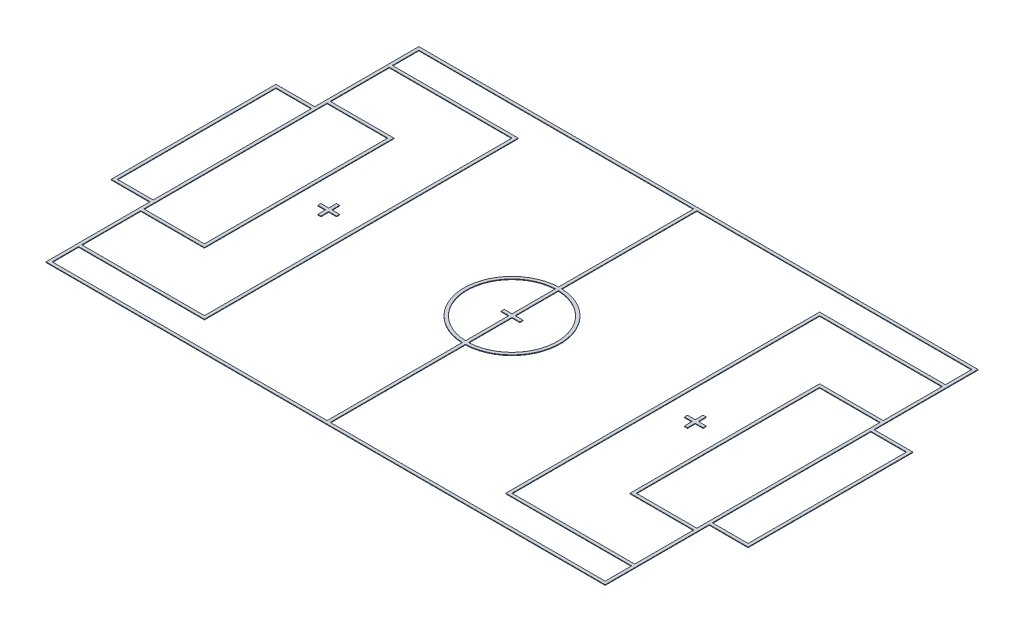
SolidWorks part; units mm, degrees
ref_plane "Front Plane" through (0, 0, 0) normal (0, 0, 1) x (1, 0, 0)
ref_plane "Top Plane" through (0, 0, 0) normal (0, 1, 0) x (1, 0, 0)
ref_plane "Right Plane" through (0, 0, 0) normal (1, 0, 0) x (0, 0, -1)
sketch "Sketch1" plane through (0, 0, 0) normal (0, 1, 0) x (1, 0, 0)
  line L0 (-4450, 2950) -> (-4450, 2525)
  line L1 (-5500, 4000) -> (5500, 4000)
  line L2 (-5500, 4000) -> (-5500, -4000)
  line L3 (-5500, -4000) -> (5500, -4000)
  line L4 (5500, 4000) -> (5500, -4000)
  line L5 (-4500, 3000) -> (4500, 3000)
  line L6 (-4500, 3000) -> (-4500, 1325)
  line L7 (-4500, -3000) -> (4500, -3000)
  line L8 (4500, 3000) -> (4500, 1325)
  line L9 (-4450, -2950) -> (-25, -2950)
  line L10 (4450, 2950) -> (4450, 2525)
  line L11 (-4450, 2950) -> (-25, 2950)
  line L12 (25, -2950) -> (4450, -2950)
  line L13 (-25, 2950) -> (-25, 773.6822)
  line L14 (25, 2950) -> (25, 773.6822)
  line L15 (-4450, -2950) -> (4450, -2950) construction
  line L16 (-25, 723.5912) -> (-25, 25)
  line L17 (25, 723.5912) -> (25, 25)
  line L18 (25, 2950) -> (4450, 2950)
  line L19 (-4450, 2950) -> (4450, 2950) construction
  line L20 (-25, -773.6822) -> (-25, -2950)
  line L21 (25, -773.6822) -> (25, -2950)
  line L22 (-150, 0) -> (150, 0) construction
  line L27 (-150, -25) -> (-25, -25)
  line L28 (-150, 25) -> (-25, 25)
  line L29 (-150, -25) -> (-150, 25)
  line L30 (150, -25) -> (150, 25)
  line L31 (25, 25) -> (150, 25)
  line L32 (-150, 25) -> (150, 25) construction
  line L33 (25, -25) -> (150, -25)
  line L34 (-150, -25) -> (150, -25) construction
  line L35 (-25, -25) -> (-25, -723.5912)
  line L36 (25, -25) -> (25, -723.5912)
  line L37 (-4450, 1500) -> (-3450, 1500) construction
  line L38 (-3450, 1500) -> (-3450, -1500) construction
  line L39 (-3450, -1500) -> (-4450, -1500) construction
  line L40 (-4450, 2500) -> (-2450, 2500) construction
  line L41 (-2450, 2500) -> (-2450, -2500) construction
  line L42 (-2450, -2500) -> (-4450, -2500) construction
  line L43 (-4450, 1475) -> (-3475, 1475)
  line L44 (-3475, 1475) -> (-3475, -1475)
  line L45 (-3475, -1475) -> (-4450, -1475)
  line L46 (-4450, 2475) -> (-2475, 2475)
  line L47 (-2475, 2475) -> (-2475, -2475)
  line L48 (-2475, -2475) -> (-4450, -2475)
  line L49 (-4450, 1525) -> (-3425, 1525)
  line L50 (-3425, 1525) -> (-3425, -1525)
  line L51 (-3425, -1525) -> (-4450, -1525)
  line L52 (-4450, 2525) -> (-2425, 2525)
  line L53 (-2425, 2525) -> (-2425, -2525)
  line L54 (-2425, -2525) -> (-4450, -2525)
  line L59 (-4450, 1475) -> (-4450, -1475)
  line L60 (-4450, 2950) -> (-4450, -2950) construction
  line L61 (-4450, 2475) -> (-4450, 1525)
  line L62 (-4450, -2525) -> (-4450, -2950)
  line L63 (-4450, -1525) -> (-4450, -2475)
  line L64 (-3100, 0) -> (-2800, 0) construction
  line L65 (-2950, 150) -> (-2950, -150) construction
  line L66 (-2975, 150) -> (-2975, 25)
  line L67 (-3100, -25) -> (-2975, -25)
  line L68 (-2925, 150) -> (-2925, 25)
  line L69 (-3100, 25) -> (-2975, 25)
  line L70 (-2975, 150) -> (-2925, 150)
  line L71 (-2975, -150) -> (-2925, -150)
  line L72 (-3100, -25) -> (-3100, 25)
  line L73 (-2800, -25) -> (-2800, 25)
  line L74 (-2975, -25) -> (-2975, -150)
  line L75 (-2975, 150) -> (-2975, -150) construction
  line L76 (-2925, 25) -> (-2800, 25)
  line L77 (-3100, 25) -> (-2800, 25) construction
  line L78 (-2925, -25) -> (-2925, -150)
  line L79 (-2925, 150) -> (-2925, -150) construction
  line L80 (-2925, -25) -> (-2800, -25)
  line L81 (-3100, -25) -> (-2800, -25) construction
  line L82 (-4500, 1300) -> (-5100, 1300) construction
  line L83 (-5100, 1300) -> (-5100, -1300) construction
  line L84 (-5100, -1300) -> (-4500, -1300) construction
  line L85 (-4500, 1325) -> (-5125, 1325)
  line L86 (-5125, 1325) -> (-5125, -1325)
  line L87 (-5125, -1325) -> (-4500, -1325)
  line L88 (-4500, 1275) -> (-5075, 1275)
  line L89 (-5075, 1275) -> (-5075, -1275)
  line L90 (-5075, -1275) -> (-4500, -1275)
  line L93 (-4500, -1325) -> (-4500, -3000)
  line L94 (-4500, 3000) -> (-4500, -3000) construction
  line L95 (-4500, 1275) -> (-4500, -1275)
  line L96 (0, 3000) -> (0, -3000) construction
  line L97 (5100, -1300) -> (4500, -1300) construction
  line L98 (5100, 1300) -> (5100, -1300) construction
  line L99 (4500, 1300) -> (5100, 1300) construction
  line L100 (2950, 150) -> (2950, -150) construction
  line L101 (3100, 0) -> (2800, 0) construction
  line L102 (2450, -2500) -> (4450, -2500) construction
  line L103 (2450, 2500) -> (2450, -2500) construction
  line L104 (4450, 2500) -> (2450, 2500) construction
  line L105 (3450, -1500) -> (4450, -1500) construction
  line L106 (3450, 1500) -> (3450, -1500) construction
  line L107 (4450, 1500) -> (3450, 1500) construction
  line L108 (4500, 1275) -> (4500, -1275)
  line L109 (5075, -1275) -> (4500, -1275)
  line L110 (5075, 1275) -> (5075, -1275)
  line L111 (4500, 1275) -> (5075, 1275)
  line L112 (5125, -1325) -> (4500, -1325)
  line L113 (5125, 1325) -> (5125, -1325)
  line L114 (4500, 1325) -> (5125, 1325)
  line L115 (2925, -25) -> (2800, -25)
  line L116 (2925, -25) -> (2925, -150)
  line L117 (2925, 25) -> (2800, 25)
  line L118 (2975, -25) -> (2975, -150)
  line L119 (2800, -25) -> (2800, 25)
  line L120 (3100, -25) -> (3100, 25)
  line L121 (2975, -150) -> (2925, -150)
  line L122 (2975, 150) -> (2925, 150)
  line L123 (3100, 25) -> (2975, 25)
  line L124 (2925, 150) -> (2925, 25)
  line L125 (3100, -25) -> (2975, -25)
  line L126 (2975, 150) -> (2975, 25)
  line L127 (2425, -2525) -> (4450, -2525)
  line L128 (2425, 2525) -> (2425, -2525)
  line L129 (4450, 2525) -> (2425, 2525)
  line L130 (3425, -1525) -> (4450, -1525)
  line L131 (3425, 1525) -> (3425, -1525)
  line L132 (4450, 1525) -> (3425, 1525)
  line L133 (2475, -2475) -> (4450, -2475)
  line L134 (2475, 2475) -> (2475, -2475)
  line L135 (4450, 2475) -> (2475, 2475)
  line L136 (3475, -1475) -> (4450, -1475)
  line L137 (3475, 1475) -> (3475, -1475)
  line L138 (4450, 1475) -> (3475, 1475)
  line L139 (4450, 2475) -> (4450, 1525)
  line L140 (4450, 2950) -> (4450, -2950) construction
  line L141 (4450, 1475) -> (4450, -1475)
  line L142 (4500, 1275) -> (4500, -1275)
  line L143 (4500, 3000) -> (4500, -3000) construction
  line L144 (4450, -1525) -> (4450, -2475)
  line L145 (4500, -1325) -> (4500, -3000)
  line L146 (4450, -2525) -> (4450, -2950)
  arc A1 (-25, 773.6822) -> (-25, -773.6822) centre (0, 0) ccw
  arc A2 (-25, 723.5912) -> (-25, -723.5912) centre (0, 0) ccw
  arc A3 (25, -773.6822) -> (25, 773.6822) centre (0, 0) ccw
  arc A6 (25, -723.5912) -> (25, 723.5912) centre (0, 0) ccw
  point P4 (0, 4000)
  point P6 (5500, 0)
  point P25 (0, 0)
  point P70 (-2950, 0)
  point P71 (-2950, 0)
  dimension "D8" = 300
  dimension "D1" = 11000
  dimension "D2" = 8000
  dimension "D3" = 1000
  dimension "D4" = 1000
  dimension "D5" = 1000
  dimension "D6" = 1000
  dimension "D11" = 3000
  dimension "D12" = 1000
  dimension "D13" = 5000
  dimension "D14" = 2000
  dimension "D17" = 300
  dimension "D18" = 300
  dimension "D19" = 1500
  dimension "D22" = 2600
  dimension "D23" = 600
  dimension "D26" = 25
  dimension "D27" = 50
  dimension "D7" = 50
  dimension "D9" = 25
  dimension "D10" = 25
  dimension "D15" = 25
  dimension "D16" = 25
  dimension "D20" = 25
  dimension "D21" = 25
  dimension "D24" = 25
  dimension "D25" = 25
extrude "Boss-Extrude2" add sketch "Sketch1" along normal blind 10 separate body contours L145 L112 L113 L114 L8 L5 L6 L85 L86 L87 L93 L7 A6 L36 L33 L30 L31 L17 A2 L16 L28 L29 L27 L35 L138 L141 L136 L137 L108 L111 L110 L109 L88 L95 L90 L89 L59 L43 L44 L45 L63 L51 L50 L49 | L78 L80 L73 L76 L68 L70 L66 L69 L72 L67 L74 L71 | L126 L122 L124 L117 L119 L115 L116 L121 L118 L125 L120 L123
